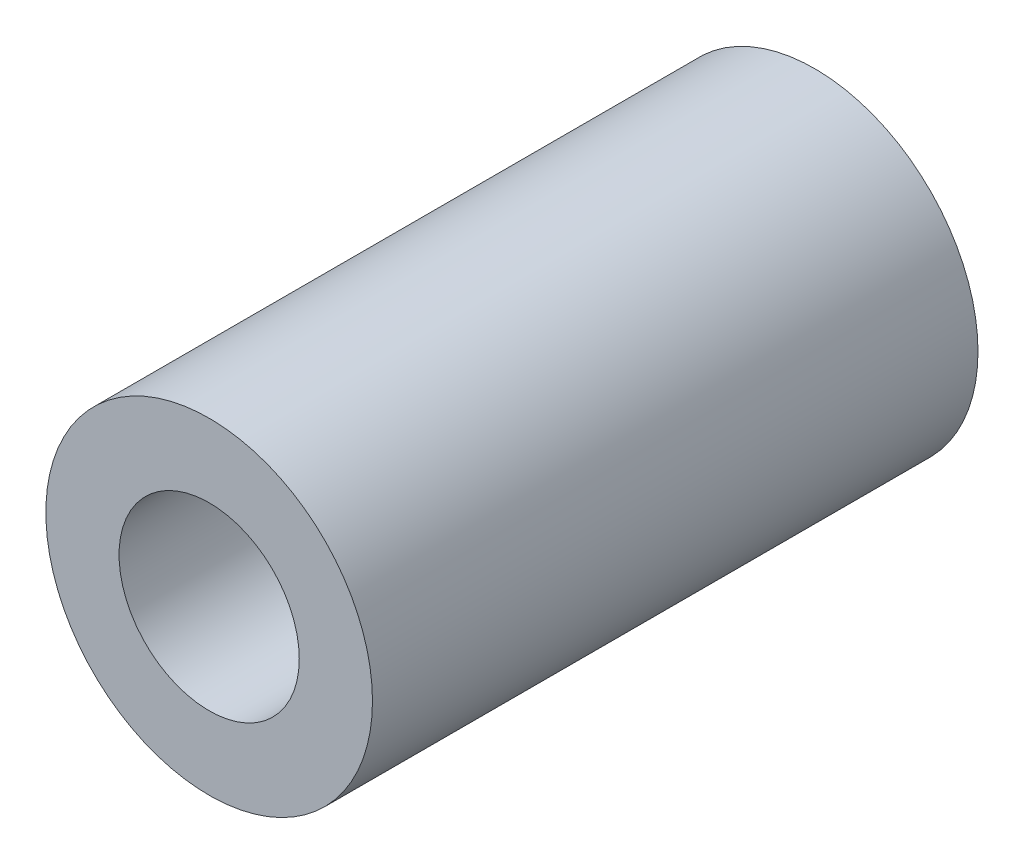
SolidWorks part; units mm, degrees
ref_plane "Front Plane" through (0, 0, 0) normal (0, 0, 1) x (1, 0, 0)
ref_plane "Top Plane" through (0, 0, 0) normal (0, 1, 0) x (1, 0, 0)
ref_plane "Right Plane" through (0, 0, 0) normal (1, 0, 0) x (0, 0, -1)
sketch "Sketch1" plane through (0, 0, 0) normal (0, 0, 1) x (1, 0, 0)
  circle A0 centre (0, 0) radius 11.5094
  dimension "D1" = 23.0188
extrude "Boss-Extrude1" add sketch "Sketch1" along normal blind 42.672
sketch "Sketch2" plane through (0, 0, 42.672) normal (0, 0, 1) x (1, 0, 0)
  circle A0 centre (0, 0) radius 6.35
extrude "Cut-Extrude1" cut sketch "Sketch2" against normal through all both and the other way through all
